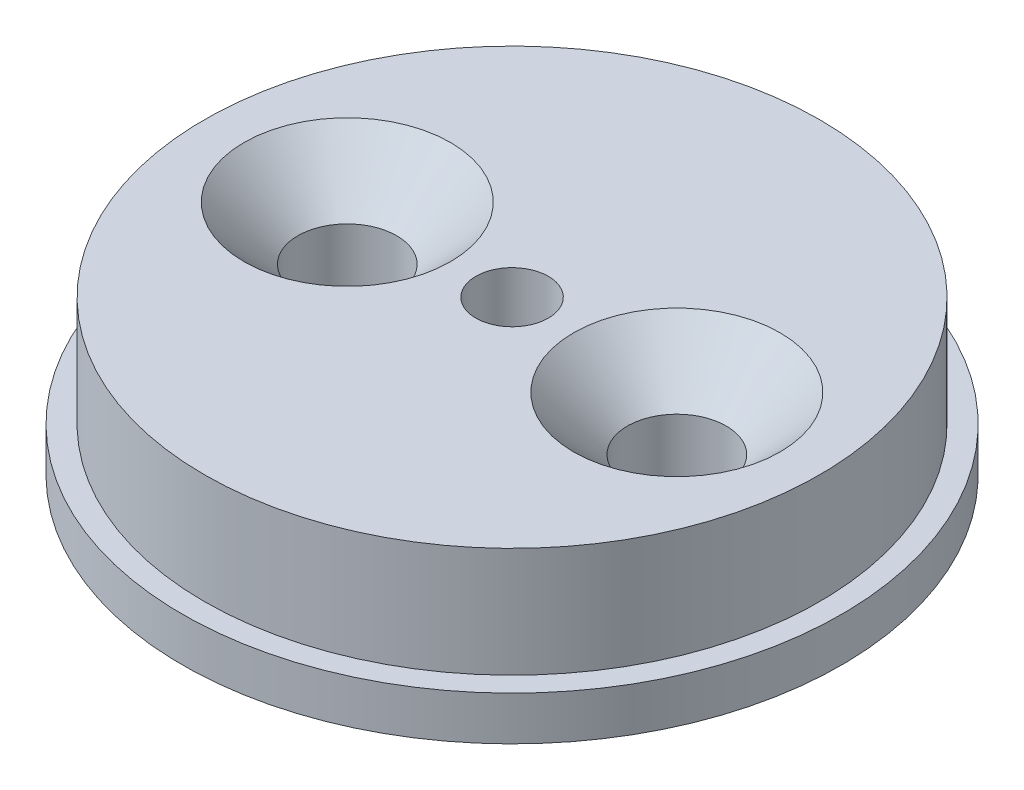
SolidWorks part; units mm, degrees
material "AISI 304"
ref_plane "정면" through (0, 0, 0) normal (0, 0, 1) x (1, 0, 0)
ref_plane "윗면" through (0, 0, 0) normal (0, 1, 0) x (1, 0, 0)
ref_plane "우측면" through (0, 0, 0) normal (1, 0, 0) x (0, 0, -1)
sketch "스케치1" plane through (0, 0, 0) normal (0, 0, 1) x (1, 0, 0)
  line L0 (0, 0) -> (0, 23.922) construction
  line L1 (0, 0) -> (-15, 0)
  line L2 (-15, 0) -> (-15, 2)
  line L3 (-15, 2) -> (-14, 2)
  line L4 (-14, 2) -> (-14, 7)
  line L5 (-14, 7) -> (0, 7)
  line L6 (0, 7) -> (0, 0)
  dimension "D1" = 30
  dimension "D2" = 28
  dimension "D3" = 2
  dimension "D4" = 5
revolve "회전1" add sketch "스케치1" angle 360 about L0
hole_wizard "M4 접시 머리 나사용 카운터싱크1" positions "스케치2" profile "스케치3" countersink size "M4" standard "ISO" end condition up to next
sketch "스케치2" plane through (0, 7, 0) normal (0, 1, 0) x (1, 0, 0)
  line L0 (-7.5, 0) -> (7.5, 0)
  circle A0 centre (0, 0) radius 14 construction
  point P0 (-7.5, 0)
  point P2 (7.5, 0)
  point P10 (0, 0)
  dimension "D1" = 15
sketch "스케치3" plane through (-7.5, 7, 0) normal (1, 0, 0) x (0, 0, 1)
  line L0 (0, 0) -> (0, 7)
  line L1 (0, 7) -> (2.25, 7)
  line L2 (2.25, 7) -> (2.25, 2.45)
  line L3 (2.25, 2.45) -> (4.7, 0)
  line L5 (4.7, 0) -> (0, 0)
  line L6 (-2.25, 2.45) -> (-4.7, 0) construction
  line L11 (0, -6.35) -> (0, 107.95) construction
  dimension "관통 구멍 지름" = 4.5
  dimension "관통 구멍 깊이" = 7
  dimension "표면 카운터싱크 지름" = 9.4
  dimension "표면 카운터싱크 각도" = 90
sketch "스케치4" plane through (0, 0, 0) normal (0, -1, 0) x (1, 0, 0)
  circle A0 centre (0, 0) radius 3.75
  dimension "D1" = 7.5
extrude "M4 둥근 머리 나사용 카운터싱크" cut sketch "스케치4" against normal blind 3
hole_wizard "M4 나사 구멍1" positions "스케치5" profile "스케치6" tap size "M4" standard "ISO" end condition up to next
sketch "스케치5" plane through (0, 3, 0) normal (0, -1, 0) x (-1, 0, 0)
  point P0 (0, 0)
sketch "스케치6" plane through (0, 3, 0) normal (1, 0, 0) x (0, 0, -1)
  line L0 (0, 0) -> (0, 4)
  line L1 (0, 4) -> (1.65, 4)
  line L2 (1.65, 4) -> (1.65, 0)
  line L5 (1.65, 0) -> (0, 0)
  line L11 (0, -6.35) -> (0, 107.95) construction
  dimension "관통 탭 드릴 지름" = 3.3
  dimension "관통 탭 드릴 깊이" = 4
cosmetic thread "구멍 나사산1"
